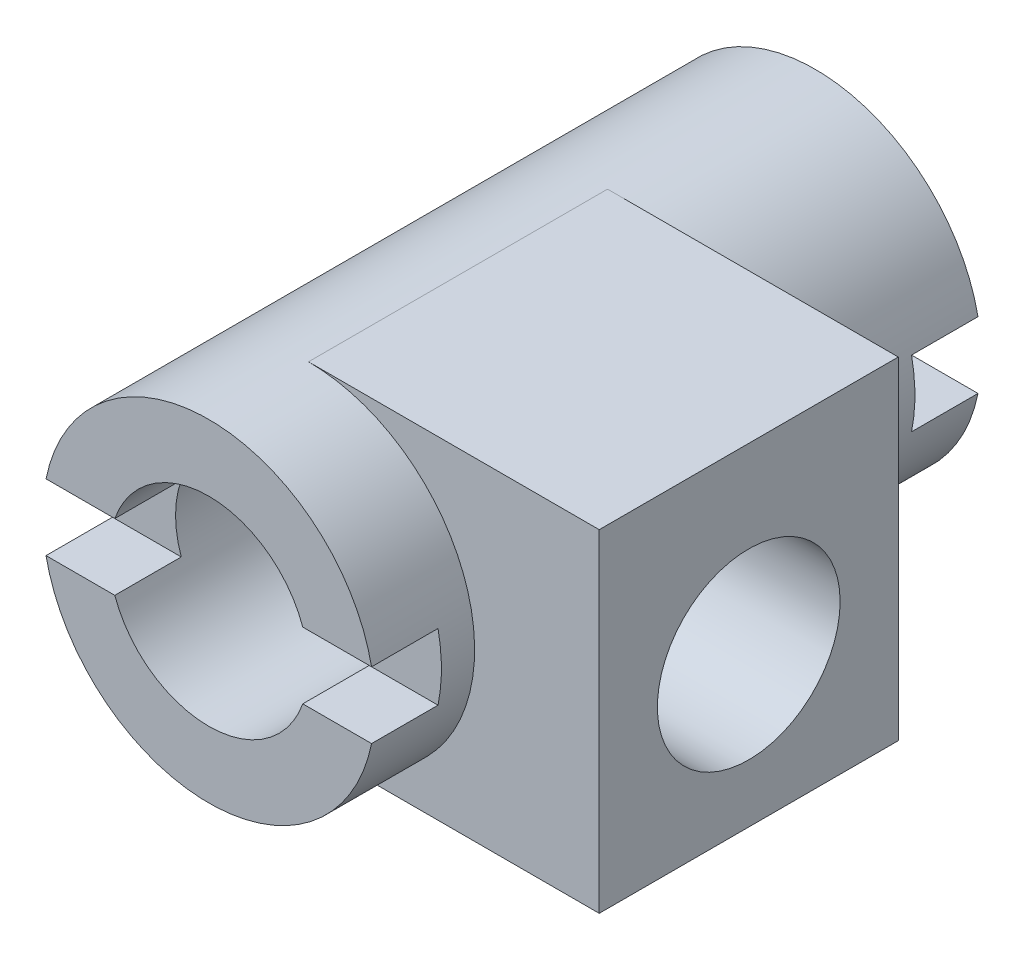
SolidWorks part; units mm, degrees
ref_plane "Front Plane" through (0, 0, 0) normal (0, 0, 1) x (1, 0, 0)
ref_plane "Top Plane" through (0, 0, 0) normal (0, 1, 0) x (1, 0, 0)
ref_plane "Right Plane" through (0, 0, 0) normal (1, 0, 0) x (0, 0, -1)
sketch "Sketch1" plane through (0, 0, 0) normal (0, 0, 1) x (1, 0, 0)
  line L0 (-58.1949, 0) -> (59.3502, 0) construction
  line L1 (0, 32.5632) -> (0, -28.0866) construction
  circle A0 centre (0, 0) radius 20
  circle A1 centre (0, 0) radius 12
  dimension "D1" = 40
  dimension "D2" = 24
extrude "Boss-Extrude1" add sketch "Sketch1" against normal blind 73
ref_plane "Plane1" through (35, 0, 0) normal (1, 0, 0) x (0, 0, -1)
sketch "Sketch2" plane through (35, 0, 0) normal (1, 0, 0) x (0, 0, -1)
  line L0 (30, 26.1772) -> (30, -34.2557) construction
  line L1 (-17.9364, 0) -> (99.7436, 0) construction
  line L2 (12, -20) -> (48, -20)
  line L3 (12, -20) -> (12, 20)
  line L4 (12, 20) -> (48, 20)
  line L5 (48, -20) -> (48, 20)
  line L6 (12, -20) -> (48, 20) construction
  line L7 (12, 20) -> (48, -20) construction
  line L8 (0, 20) -> (0, -20) construction
  circle A1 centre (30, -2) radius 11
  point P3 (30, 0)
  point P15 (0, 0)
  dimension "D2" = 18
  dimension "D4" = 22
  dimension "D1" = 36
  dimension "D3" = 40
  dimension "D5" = 12
extrude "Boss-Extrude2" add sketch "Sketch2" against normal up to surface (15.1003 mm away)
sketch "Sketch4" plane through (0, 0, 0) normal (0, 0, 1) x (1, 0, 0)
  line L0 (-35.1165, 0) -> (39.4445, 0) construction
  line L1 (0, 26.0984) -> (0, -29.0524) construction
  line L3 (-25.8709, 4) -> (22.4526, 4)
  line L4 (-25.8709, 4) -> (-25.8709, -4)
  line L5 (-25.8709, -4) -> (22.4526, -4)
  line L6 (22.4526, 4) -> (22.4526, -4)
  circle A2 centre (0, 0) radius 12 construction
  dimension "D1" = 8
  dimension "D2" = 22.4526
  dimension "D3" = 25.8709
extrude "Cut-Extrude1" cut sketch "Sketch4" against normal blind 8
sketch "Sketch5" plane through (0, 0, -73) normal (0, 0, -1) x (-1, 0, 0)
  line L0 (-42.775, 0) -> (29.5656, 0) construction
  line L1 (0, 24.03) -> (0, -28.3275) construction
  line L3 (-21.293, -4) -> (21.293, -4)
  line L4 (-21.293, -4) -> (-21.293, 4)
  line L5 (-21.293, 4) -> (21.293, 4)
  line L6 (21.293, -4) -> (21.293, 4)
  circle A1 centre (0, 0) radius 12 construction
  dimension "D1" = 8
  dimension "D2" = 21.293
extrude "Cut-Extrude2" cut sketch "Sketch5" against normal blind 8
